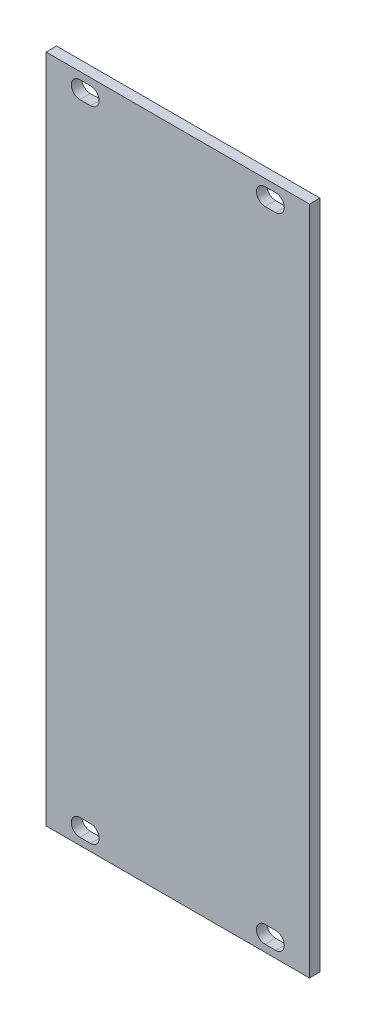
SolidWorks part; units mm, degrees
ref_plane "Front Plane" through (0, 0, 0) normal (0, 0, 1) x (1, 0, 0)
ref_plane "Top Plane" through (0, 0, 0) normal (0, 1, 0) x (1, 0, 0)
ref_plane "Right Plane" through (0, 0, 0) normal (1, 0, 0) x (0, 0, -1)
sketch "Sketch1" plane through (0, 0, 0) normal (0, 0, 1) x (1, 0, 0)
  line L0 (-17.75, 64.25) -> (-17.75, -64.25) construction
  line L1 (-25.25, 64.25) -> (25.25, 64.25)
  line L2 (-25.25, 64.25) -> (-25.25, -64.25)
  line L3 (-25.25, -64.25) -> (25.25, -64.25)
  line L4 (25.25, 64.25) -> (25.25, -64.25)
  line L5 (-25.25, 64.25) -> (25.25, -64.25) construction
  line L6 (-25.25, -64.25) -> (25.25, 64.25) construction
  line L7 (-25.25, 61.25) -> (25.25, 61.25) construction
  line L8 (-25.25, -61.25) -> (25.25, -61.25) construction
  line L9 (-18.766, -61.25) -> (-16.734, -61.25) construction
  line L10 (16.734, 61.25) -> (18.766, 61.25) construction
  line L11 (-18.766, -59.6) -> (-16.734, -59.6)
  line L12 (-18.766, -62.9) -> (-16.734, -62.9)
  line L13 (-18.766, 61.25) -> (-16.734, 61.25) construction
  line L14 (-18.766, 62.9) -> (-16.734, 62.9)
  line L15 (-18.766, 59.6) -> (-16.734, 59.6)
  line L16 (16.734, 62.9) -> (18.766, 62.9)
  line L17 (16.734, 59.6) -> (18.766, 59.6)
  line L18 (16.734, -61.25) -> (18.766, -61.25) construction
  line L19 (16.734, -59.6) -> (18.766, -59.6)
  line L20 (16.734, -62.9) -> (18.766, -62.9)
  line L21 (17.75, 64.25) -> (17.75, -64.25) construction
  arc A0 (-18.766, -59.6) -> (-18.766, -62.9) centre (-18.766, -61.25) ccw
  arc A1 (-16.734, -62.9) -> (-16.734, -59.6) centre (-16.734, -61.25) ccw
  arc A2 (-18.766, 62.9) -> (-18.766, 59.6) centre (-18.766, 61.25) ccw
  arc A3 (-16.734, 59.6) -> (-16.734, 62.9) centre (-16.734, 61.25) ccw
  arc A4 (16.734, 62.9) -> (16.734, 59.6) centre (16.734, 61.25) ccw
  arc A5 (18.766, 59.6) -> (18.766, 62.9) centre (18.766, 61.25) ccw
  arc A6 (16.734, -59.6) -> (16.734, -62.9) centre (16.734, -61.25) ccw
  arc A7 (18.766, -62.9) -> (18.766, -59.6) centre (18.766, -61.25) ccw
  point P0 (0, 0)
  point P8 (17.75, 61.25)
  point P18 (-17.75, -61.25)
  point P24 (-17.75, 61.25)
  point P34 (17.75, -61.25)
  point P42 (0, 0)
  point P43 (0, 0)
  dimension "D6" = 1.65
  dimension "D7" = 1.65
  dimension "D11" = 1.65
  dimension "D13" = 1.65
  dimension "D1" = 128.5
  dimension "D2" = 50.5
  dimension "D3" = 7.5
  dimension "D4" = 3
  dimension "D8" = 2.032
  dimension "D9" = 2.032
  dimension "D10" = 7.5
  dimension "D12" = 2.032
  dimension "D14" = 2.032
  dimension "D5" = 3
extrude "Boss-Extrude1" add sketch "Sketch1" along normal blind 2
